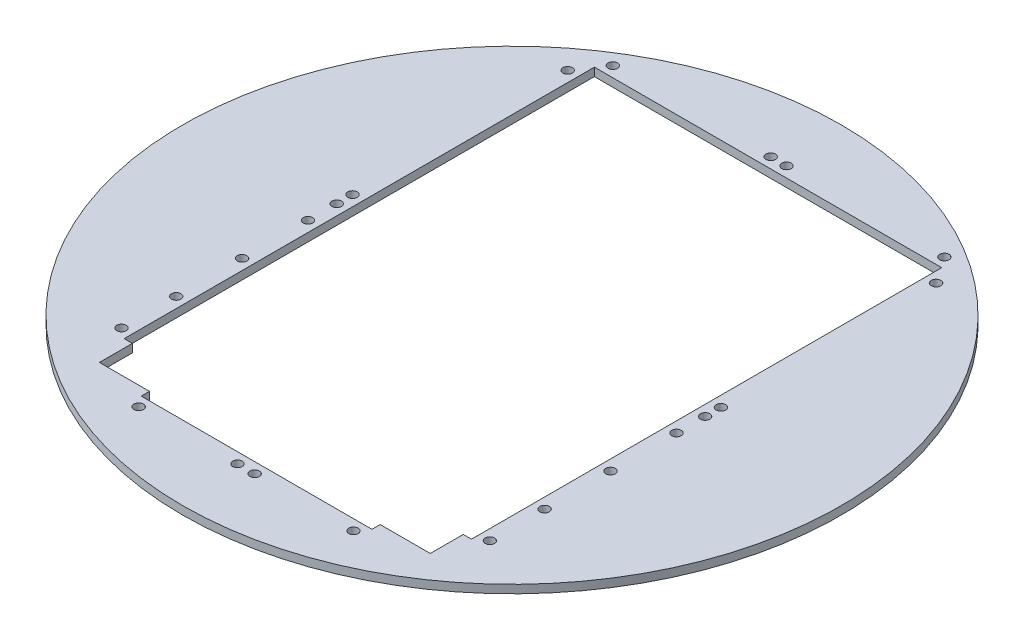
SolidWorks part; units mm, degrees
ref_plane "Front" through (0, 0, 0) normal (0, 0, 1) x (1, 0, 0)
ref_plane "Top" through (0, 0, 0) normal (0, 1, 0) x (1, 0, 0)
ref_plane "Right" through (0, 0, 0) normal (1, 0, 0) x (0, 0, -1)
sketch "Sketch1" plane through (0, 0, 0) normal (0, 1, 0) x (1, 0, 0)
  circle A0 centre (0, 0) radius 127
  dimension "D1" = 254
extrude "Boss-Extrude1" add sketch "Sketch1" along normal blind 3.175
sketch "Sketch2" plane through (0, 3.175, 0) normal (0, 1, 0) x (1, 0, 0)
  line L1 (63.5, -95.25) -> (-63.5, -95.25)
  line L2 (63.5, -95.25) -> (63.5, 95.25)
  line L3 (63.5, 95.25) -> (-63.5, 95.25)
  line L4 (-63.5, -95.25) -> (-63.5, 95.25)
  line L5 (63.5, -95.25) -> (-63.5, 95.25) construction
  line L6 (63.5, 95.25) -> (-63.5, -95.25) construction
  point P0 (0, 0)
  dimension "D1" = 127
  dimension "D2" = 190.5
extrude "Cut-Extrude1" cut sketch "Sketch2" against normal blind 3.175
sketch "Sketch3" plane through (0, 3.175, 0) normal (0, 1, 0) x (1, 0, 0)
  line L0 (0, -95.25) -> (0, 0) construction
  line L1 (-63.5, -95.25) -> (63.5, -95.25) construction
  line L2 (-57.15, -62.865) -> (-57.15, -95.25)
  line L3 (-57.15, -95.25) -> (57.15, -95.25)
  line L4 (57.15, -95.25) -> (57.15, -62.865)
  line L5 (57.15, -62.865) -> (-57.15, -62.865)
  line L7 (0, -95.25) -> (-57.15, -62.865) construction
  line L8 (57.15, -62.865) -> (0, -95.25) construction
  dimension "D1" = 32.385
  dimension "D2" = 114.3
extrude "Boss-Extrude2" add sketch "Sketch3" against normal blind 3.175
sketch "Sketch4" plane through (0, 0, 0) normal (0, -1, 0) x (1, 0, 0)
  line L0 (-57.15, 95.25) -> (-50.8, 95.25) construction
  line L1 (0, 88.9) -> (0, 127) construction
  line L2 (-57.15, 95.25) -> (-57.15, 88.9) construction
  line L3 (-57.15, 88.9) -> (57.15, 88.9) construction
  line L4 (57.15, 88.9) -> (57.15, 95.25) construction
  line L5 (-57.15, 92.075) -> (57.15, 92.075) construction
  line L8 (50.8, 92.075) -> (50.8, 98.425)
  line L9 (50.8, 98.425) -> (-50.8, 98.425)
  line L10 (-50.8, 92.075) -> (-50.8, 98.425)
  line L11 (0, 92.075) -> (-50.8, 98.425) construction
  line L12 (50.8, 98.425) -> (0, 92.075) construction
  line L13 (50.8, 92.075) -> (-50.8, 92.075)
  line L14 (50.8, 95.25) -> (57.15, 95.25) construction
  circle A0 centre (0, 0) radius 127 construction
  point P13 (0, 92.075)
  dimension "D1" = 6.35
  dimension "D2" = 101.6
extrude "Cut-Extrude2" cut sketch "Sketch4" against normal blind 3.175
sketch "Sketch5" plane through (0, 0, 0) normal (0, -1, 0) x (1, 0, 0)
  line L0 (50.8, 92.075) -> (50.8, 98.425) construction
  line L1 (-50.8, 92.075) -> (50.8, 92.075)
  line L2 (-50.8, 92.075) -> (-50.8, 95.25)
  line L3 (-50.8, 95.25) -> (50.8, 95.25)
  line L4 (50.8, 92.075) -> (50.8, 95.25)
extrude "Boss-Extrude5" add sketch "Sketch5" against normal through all
sketch "Sketch6" plane through (0, 0, 0) normal (0, -1, 0) x (1, 0, 0)
  line L1 (-57.15, 62.865) -> (57.15, 62.865)
  line L2 (-57.15, 62.865) -> (-57.15, 95.25)
  line L3 (-57.15, 95.25) -> (57.15, 95.25)
  line L4 (57.15, 62.865) -> (57.15, 95.25)
extrude "Cut-Extrude3" cut sketch "Sketch6" against normal through all
sketch "Sketch7" plane through (0, 0, 0) normal (0, -1, 0) x (1, 0, 0)
  line L0 (-50.8, 98.425) -> (-47.752, 98.425) construction
  line L1 (50.8, 98.425) -> (-50.8, 98.425) construction
  line L2 (-47.752, 98.425) -> (-47.752, 102.489) construction
  line L3 (0, 98.425) -> (0, 127) construction
  line L4 (0, 98.425) -> (-3.302, 98.425) construction
  line L5 (-3.302, 98.425) -> (-3.302, 102.489) construction
  circle A0 centre (-47.752, 102.489) radius 1.8288
  circle A1 centre (0, 0) radius 127 construction
  circle A2 centre (-3.302, 102.489) radius 1.8288
  circle A3 centre (3.302, 102.489) radius 1.8288
  circle A4 centre (47.752, 102.489) radius 1.8288
  dimension "D3" = 3.6576
  dimension "D6" = 3.6576
  dimension "D1" = 3.048
  dimension "D2" = 4.064
  dimension "D4" = 4.064
  dimension "D5" = 3.302
extrude "Cut-Extrude4" cut sketch "Sketch7" against normal through all
sketch "Sketch8" plane through (0, 0, 0) normal (0, -1, 0) x (1, 0, 0)
  line L0 (50.8, 98.425) -> (-50.8, 98.425) construction
  line L1 (-50.8, 95.25) -> (-44.45, 95.25)
  line L2 (-50.8, 95.25) -> (-50.8, 98.425)
  line L3 (-50.8, 98.425) -> (-44.45, 98.425)
  line L4 (-44.45, 95.25) -> (-44.45, 98.425)
  line L6 (50.8, 95.25) -> (44.45, 95.25)
  line L7 (50.8, 95.25) -> (50.8, 98.425)
  line L8 (50.8, 98.425) -> (44.45, 98.425)
  line L9 (44.45, 95.25) -> (44.45, 98.425)
  dimension "D1" = 6.35
  dimension "D2" = 6.35
extrude "Boss-Extrude6" add sketch "Sketch8" against normal blind 3.175
sketch "Sketch9" plane through (0, 0, 0) normal (0, -1, 0) x (1, 0, 0)
  line L0 (-44.45, 98.425) -> (-41.402, 98.425) construction
  line L1 (44.45, 98.425) -> (-44.45, 98.425) construction
  line L2 (-41.402, 98.425) -> (-41.402, 102.489) construction
  line L3 (44.45, 98.425) -> (41.402, 98.425) construction
  line L4 (41.402, 98.425) -> (41.402, 102.489) construction
  circle A0 centre (-41.402, 102.489) radius 1.8288
  circle A1 centre (41.402, 102.489) radius 1.8288
  dimension "D5" = 3.6576
  dimension "D6" = 3.6576
  dimension "D1" = 3.048
  dimension "D2" = 4.064
  dimension "D3" = 3.048
  dimension "D4" = 4.064
extrude "Cut-Extrude5" cut sketch "Sketch9" against normal blind 3.175
sketch "Sketch10" plane through (0, 0, 0) normal (0, -1, 0) x (1, 0, 0)
  circle A0 centre (-47.752, 102.489) radius 1.8288
  circle A1 centre (47.752, 102.489) radius 1.8288
  dimension "D1" = 3.6576
  dimension "D2" = 3.6576
extrude "Boss-Extrude7" add sketch "Sketch10" against normal blind 3.175
sketch "Sketch11" plane through (0, 0, 0) normal (0, -1, 0) x (1, 0, 0)
  line L6 (-63.754, 95.25) -> (-63.5, 95.25)
  line L7 (63.754, 95.25) -> (63.5, 95.25)
  line L8 (63.5, 95.25) -> (63.5, -95.25)
  line L9 (63.754, 95.25) -> (63.754, -95.504)
  line L10 (63.754, -95.504) -> (-63.754, -95.504)
  line L11 (-63.754, -95.504) -> (-63.754, 95.25)
  line L12 (63.754, 95.25) -> (63.754, -95.504)
  line L13 (63.754, -95.504) -> (-63.754, -95.504)
  line L14 (-63.754, -95.504) -> (-63.754, 95.25)
  line L15 (63.5, -95.25) -> (-63.5, -95.25)
  line L16 (-63.5, -95.25) -> (-63.5, 95.25)
  dimension "D1" = 0.254
extrude "Cut-Extrude6" cut sketch "Sketch11" against normal through all
sketch "Sketch13" plane through (0, 0, 0) normal (0, -1, 0) x (1, 0, 0)
  line L1 (-63.754, -95.504) -> (-66.929, -95.504)
  line L2 (-63.754, -95.504) -> (-63.754, 82.55)
  line L3 (-63.754, 82.55) -> (-66.929, 82.55)
  line L4 (-66.929, -95.504) -> (-66.929, 82.55)
  line L5 (63.754, -95.504) -> (66.929, -95.504)
  line L6 (63.754, -95.504) -> (63.754, 82.55)
  line L7 (63.754, 82.55) -> (66.929, 82.55)
  line L8 (66.929, -95.504) -> (66.929, 82.55)
  dimension "D1" = 3.175
  dimension "D2" = 3.175
  dimension "D3" = 178.054
  dimension "D4" = 178.054
extrude "Cut-Extrude8" cut sketch "Sketch13" against normal through all
sketch "Sketch14" plane through (0, 0, 0) normal (0, -1, 0) x (1, 0, 0)
  line L0 (0, 127) -> (0, -127) construction
  line L1 (-66.929, 82.55) -> (-66.929, 79.502) construction
  line L2 (-66.929, 82.55) -> (-66.929, -95.504) construction
  line L3 (-66.929, 79.502) -> (-70.993, 79.502) construction
  line L4 (-66.929, -95.504) -> (-66.929, -92.456) construction
  line L5 (-66.929, -92.456) -> (-70.993, -92.456) construction
  line L6 (-70.993, 79.502) -> (-70.993, -3.429) construction
  line L7 (-70.993, -92.456) -> (-70.993, -9.525) construction
  circle A0 centre (0, 0) radius 127 construction
  circle A1 centre (-70.993, 79.502) radius 1.8288
  circle A2 centre (-70.993, -92.456) radius 1.8288
  circle A3 centre (-70.993, -3.429) radius 1.8288
  circle A4 centre (-70.993, -9.525) radius 1.8288
  circle A5 centre (70.993, -92.456) radius 1.8288
  circle A6 centre (70.993, -9.525) radius 1.8288
  circle A7 centre (70.993, -3.429) radius 1.8288
  circle A8 centre (70.993, 79.502) radius 1.8288
  dimension "D3" = 3.6576
  dimension "D6" = 3.6576
  dimension "D9" = 3.6576
  dimension "D10" = 3.6576
  dimension "D1" = 3.048
  dimension "D2" = 4.064
  dimension "D4" = 3.048
  dimension "D5" = 4.064
  dimension "D7" = 82.931
  dimension "D8" = 82.931
extrude "Cut-Extrude9" cut sketch "Sketch14" against normal through all
sketch "Sketch15" plane through (0, 0, 0) normal (0, -1, 0) x (1, 0, 0)
  line L0 (-66.929, -95.504) -> (66.929, -95.504)
  line L1 (-66.929, -95.504) -> (-66.929, -98.679)
  line L2 (66.929, -95.504) -> (66.929, -98.679)
  line L3 (-66.929, -98.679) -> (66.929, -98.679)
  dimension "D1" = 3.175
extrude "Cut-Extrude10" cut sketch "Sketch15" against normal through all
sketch "Sketch16" plane through (0, 0, 0) normal (0, -1, 0) x (1, 0, 0)
  line L0 (-66.929, -98.679) -> (-63.881, -98.679) construction
  line L1 (-66.929, -98.679) -> (66.929, -98.679) construction
  line L2 (-63.881, -98.679) -> (-63.881, -102.743) construction
  line L3 (0, 127) -> (0, -127) construction
  line L4 (0, -98.679) -> (-3.048, -98.679) construction
  line L5 (-3.048, -98.679) -> (-3.048, -102.743) construction
  circle A0 centre (-63.881, -102.743) radius 1.8288
  circle A1 centre (0, 0) radius 127 construction
  circle A2 centre (-3.048, -102.743) radius 1.8288
  circle A3 centre (3.048, -102.743) radius 1.8288
  circle A4 centre (63.881, -102.743) radius 1.8288
  dimension "D5" = 3.6576
  dimension "D6" = 3.6576
  dimension "D1" = 3.048
  dimension "D2" = 4.064
  dimension "D3" = 4.064
  dimension "D4" = 3.048
extrude "Cut-Extrude11" cut sketch "Sketch16" against normal through all
sketch "Sketch17" plane through (0, 0, 0) normal (0, -1, 0) x (1, 0, 0)
  line L0 (-70.993, 33.02) -> (-70.993, 58.42) construction
  line L1 (-70.993, -3.429) -> (-70.993, 7.62) construction
  line L2 (-70.993, 7.62) -> (-70.993, 33.02) construction
  line L3 (0, 127) -> (0, -127) construction
  circle A0 centre (-70.993, 7.62) radius 1.8288
  circle A1 centre (-70.993, 58.42) radius 1.8288
  circle A2 centre (-70.993, 33.02) radius 1.8288
  circle A3 centre (0, 0) radius 127 construction
  circle A4 centre (70.993, 58.42) radius 1.8288
  circle A5 centre (70.993, 7.62) radius 1.8288
  circle A6 centre (70.993, 33.02) radius 1.8288
  dimension "D3" = 3.6576
  dimension "D4" = 3.6576
  dimension "D6" = 3.6576
  dimension "D1" = 25.4
  dimension "D2" = 11.049
  dimension "D5" = 25.4
extrude "Cut-Extrude12" cut sketch "Sketch17" against normal through all
